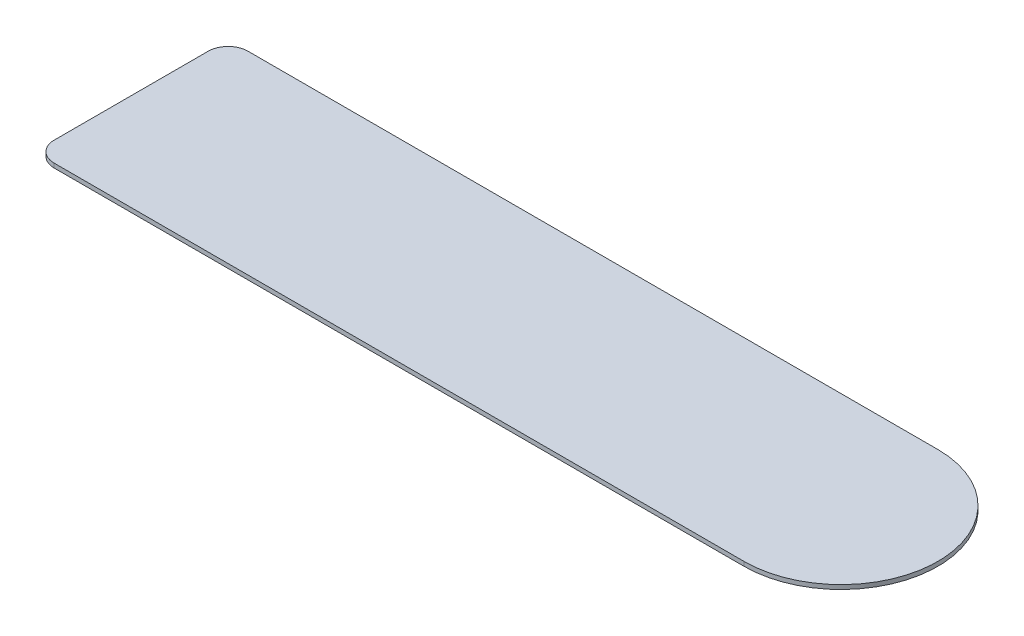
SolidWorks part; units mm, degrees
ref_plane "Front Plane" through (0, 0, 0) normal (0, 0, 1) x (1, 0, 0)
ref_plane "Top Plane" through (0, 0, 0) normal (0, 1, 0) x (1, 0, 0)
ref_plane "Right Plane" through (0, 0, 0) normal (1, 0, 0) x (0, 0, -1)
sketch "Sketch1" plane through (0, 0, 0) normal (0, 1, 0) x (1, 0, 0)
  line L0 (360, 34) -> (118, 34)
  line L1 (111, 27) -> (111, -27)
  line L2 (118, -34) -> (360, -34)
  arc A0 (111, 27) -> (118, 34) centre (118, 27) cw
  arc A2 (118, -34) -> (111, -27) centre (118, -27) cw
  arc A5 (360, -34) -> (360, 34) centre (360, 0) ccw
extrude "Boss-Extrude1" add sketch "Sketch1" along normal blind 1.5
